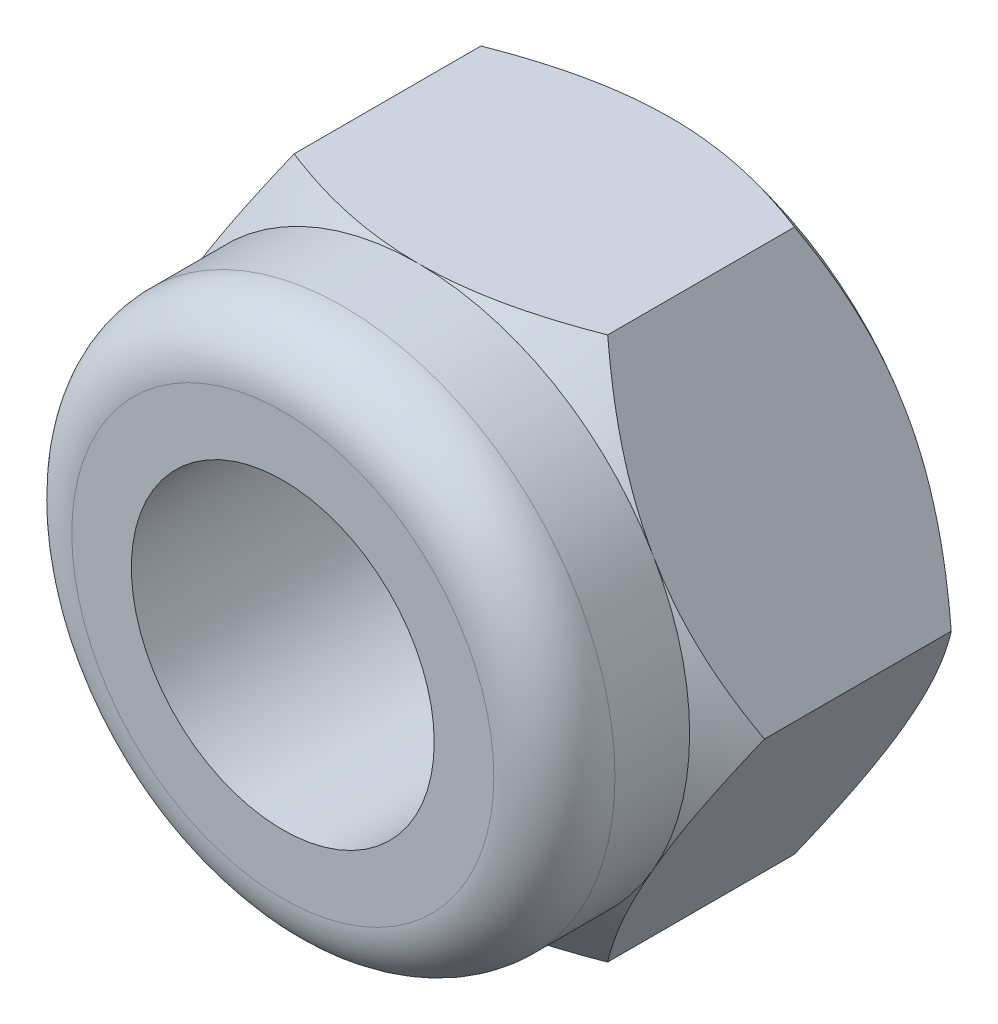
SolidWorks part; units mm, degrees
ref_plane "Front Plane" through (0, 0, 0) normal (0, 0, 1) x (1, 0, 0)
ref_plane "Top Plane" through (0, 0, 0) normal (0, 1, 0) x (1, 0, 0)
ref_plane "Right Plane" through (0, 0, 0) normal (1, 0, 0) x (0, 0, -1)
sketch "Sketch1" plane through (0, 0, 0) normal (0, 0, 1) x (1, 0, 0)
  line L0 (0, 3.1061) -> (0, 0) construction
  line L1 (0, 0) -> (3.1061, 0) construction
  line L2 (-1.5531, 2.69) -> (1.5531, 2.69)
  line L3 (1.5531, 2.69) -> (3.1061, 0)
  line L4 (1.5531, -2.69) -> (3.1061, 0)
  line L5 (-1.5531, -2.69) -> (1.5531, -2.69)
  line L6 (-1.5531, 2.69) -> (-3.1061, 0)
  line L7 (-1.5531, -2.69) -> (-3.1061, 0)
  circle A0 centre (0, 0) radius 3.1061 construction
  circle A1 centre (0, 0) radius 2.69 construction
  circle A2 centre (0, 0) radius 1.5
  point P12 (0, 2.69)
  point P14 (0, -2.69)
  dimension "D1" = 5.38
  dimension "D2" = 3
extrude "Boss-Extrude1" add sketch "Sketch1" along normal blind 2.5
sketch "Sketch2" plane through (0, 0, 2.5) normal (0, 0, 1) x (1, 0, 0)
  line L0 (-1.5531, 2.69) -> (-3.1061, 0) construction
  circle A0 centre (0, 0) radius 2.69
  circle A1 centre (0, 0) radius 1.5 construction
  circle A2 centre (0, 0) radius 1.5
extrude "Boss-Extrude2" add sketch "Sketch2" along normal blind 1.34
fillet "Fillet1" radius 0.6 1 edges at (2.69, 0, 3.84)
sketch "Sketch3" plane through (0, 0, 0) normal (1, 0, 0) x (0, 0, -1)
  line L0 (-2.5, 2.69) -> (-2.1098, 3.19)
  line L1 (-2.1098, 3.19) -> (-0.3902, 3.19)
  line L2 (-0.3902, 3.19) -> (0, 2.69)
  line L3 (0, 2.69) -> (0, 3.3251)
  line L4 (0, 3.3251) -> (-2.5, 3.3251)
  line L5 (-2.5, 3.3251) -> (-2.5, 2.69)
  line L6 (-2.5, 2.69) -> (0, 2.69) construction
  line L8 (0, 0) -> (1.9305, 0) construction
  point P9 (-1.25, 3.3251)
  point P14 (-1.25, 3.19)
  dimension "D1" = 0.5
revolve "Cut-Revolve1" cut sketch "Sketch3" angle 360 about L8
chamfer "Chamfer1" distance 0.3 angle 45 1 edges at (1.5, 0, 0)
